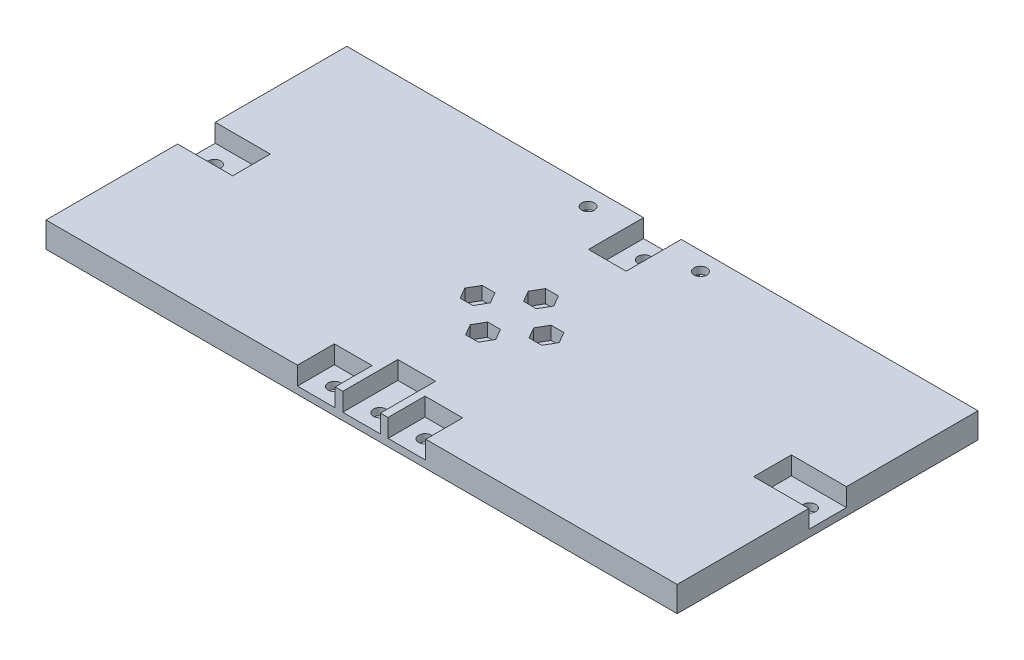
SolidWorks part; units mm, degrees
ref_plane "Front Plane" through (0, 0, 0) normal (0, 0, 1) x (1, 0, 0)
ref_plane "Top Plane" through (0, 0, 0) normal (0, 1, 0) x (1, 0, 0)
ref_plane "Right Plane" through (0, 0, 0) normal (1, 0, 0) x (0, 0, -1)
sketch "Sketch1" plane through (0, 0, 0) normal (0, 1, 0) x (1, 0, 0)
  line L1 (0, 0) -> (174.17, 0)
  line L2 (0, 0) -> (0, 83)
  line L3 (0, 83) -> (174.17, 83)
  line L4 (174.17, 0) -> (174.17, 83)
  dimension "D1" = 174.17
  dimension "D2" = 83
extrude "Boss-Extrude1" add sketch "Sketch1" along normal blind 7
sketch "Sketch2" plane through (0, 7, 0) normal (0, 1, 0) x (1, 0, 0)
  line L0 (0, 83) -> (174.17, 0) construction
  line L1 (77.585, 41.5) -> (96.585, 41.5) construction
  line L2 (87.085, 49.5) -> (87.085, 33.5) construction
  circle A0 centre (87.085, 49.5) radius 1.75
  circle A1 centre (77.585, 41.5) radius 1.75
  circle A2 centre (96.585, 41.5) radius 1.75
  circle A3 centre (87.085, 33.5) radius 1.75
  point P8 (87.085, 41.5)
  point P9 (87.085, 41.5)
  point P10 (87.085, 41.5)
  dimension "D3" = 3.5
  dimension "D1" = 19
  dimension "D2" = 16
extrude "Cut-Extrude1" cut sketch "Sketch2" against normal through all
sketch "Sketch3" plane through (0, 7, 0) normal (0, 1, 0) x (1, 0, 0)
  line L0 (0, 83) -> (174.17, 0) construction
  line L1 (5, 41.5) -> (169.17, 41.5) construction
  line L2 (87.085, 78) -> (87.085, 5) construction
  circle A0 centre (87.085, 78) radius 1.75
  circle A1 centre (5, 41.5) radius 1.75
  circle A2 centre (87.085, 5) radius 1.75
  circle A3 centre (169.17, 41.5) radius 1.75
  point P8 (87.085, 41.5)
  point P9 (87.085, 41.5)
  point P11 (87.085, 41.5)
  dimension "D3" = 3.5
  dimension "D1" = 164.17
  dimension "D2" = 73
extrude "Cut-Extrude2" cut sketch "Sketch3" against normal through all
sketch "Sketch4" plane through (0, 7, 0) normal (0, 1, 0) x (1, 0, 0)
  line L0 (0, 83) -> (0, 0) construction
  line L1 (0, 46.5) -> (15, 46.5) construction
  line L2 (0, 46.5) -> (0, 36.5) construction
  line L3 (0, 36.5) -> (15, 36.5) construction
  line L4 (15, 46.5) -> (15, 36.5) construction
  line L5 (0, 0) -> (174.17, 0) construction
  line L6 (82.085, 0) -> (92.085, 0) construction
  line L7 (82.085, 0) -> (82.085, 15) construction
  line L8 (82.085, 15) -> (92.085, 15) construction
  line L9 (92.085, 0) -> (92.085, 15) construction
  line L10 (174.17, 83) -> (0, 83) construction
  line L11 (92.085, 83) -> (82.085, 83) construction
  line L12 (92.085, 83) -> (92.085, 68) construction
  line L13 (92.085, 68) -> (82.085, 68) construction
  line L14 (82.085, 83) -> (82.085, 68) construction
  line L15 (174.17, 0) -> (174.17, 83) construction
  line L16 (174.17, 36.5) -> (159.17, 36.5) construction
  line L17 (174.17, 36.5) -> (174.17, 46.5) construction
  line L18 (174.17, 46.5) -> (159.17, 46.5) construction
  line L19 (159.17, 36.5) -> (159.17, 46.5) construction
  line L20 (0, 41.5) -> (174.17, 41.5) construction
  line L21 (87.085, 83) -> (87.085, 0) construction
  line L22 (-0.2, 46.7) -> (15.2, 46.7)
  line L23 (15.2, 46.7) -> (15.2, 36.3)
  line L24 (-0.2, 36.3) -> (15.2, 36.3)
  line L25 (-0.2, 46.7) -> (-0.2, 36.3)
  line L26 (81.885, 15.2) -> (92.285, 15.2)
  line L27 (92.285, -0.2) -> (92.285, 15.2)
  line L28 (81.885, -0.2) -> (92.285, -0.2)
  line L29 (81.885, -0.2) -> (81.885, 15.2)
  line L30 (81.885, 83.2) -> (81.885, 67.8)
  line L31 (92.285, 67.8) -> (81.885, 67.8)
  line L32 (92.285, 83.2) -> (92.285, 67.8)
  line L33 (92.285, 83.2) -> (81.885, 83.2)
  line L34 (174.37, 46.7) -> (158.97, 46.7)
  line L35 (158.97, 36.3) -> (158.97, 46.7)
  line L36 (174.37, 36.3) -> (158.97, 36.3)
  line L37 (174.37, 36.3) -> (174.37, 46.7)
  point P26 (87.085, 0)
  point P27 (0, 41.5)
  point P28 (87.085, 83)
  point P29 (174.17, 41.5)
  dimension "D1" = 15
  dimension "D2" = 10
  dimension "D3" = 0.2
extrude "Cut-Extrude3" cut sketch "Sketch4" against normal blind 5
sketch "Sketch5" plane through (0, 7, 0) normal (0, 1, 0) x (1, 0, 0)
  line L0 (0, 0) -> (81.885, 0) construction
  line L6 (79.585, 10) -> (79.585, 0) construction
  line L7 (79.585, 0) -> (69.585, 0) construction
  line L9 (79.585, 10) -> (69.585, 10) construction
  line L10 (69.585, 0) -> (69.585, 10) construction
  line L11 (94.585, 0) -> (104.585, 0) construction
  line L13 (94.585, 10) -> (104.585, 10) construction
  line L14 (104.585, 0) -> (104.585, 10) construction
  line L16 (92.285, 0) -> (174.17, 0) construction
  line L17 (94.585, 10) -> (94.585, 0) construction
  line L18 (79.585, 0) -> (94.585, 0) construction
  line L22 (87.085, 83) -> (87.085, 0) construction
  line L23 (92.285, 83) -> (81.885, 83) construction
  line L24 (79.785, 10.2) -> (69.385, 10.2)
  line L25 (69.385, -0.2) -> (69.385, 10.2)
  line L26 (79.785, -0.2) -> (69.385, -0.2)
  line L27 (79.785, 10.2) -> (79.785, -0.2)
  line L28 (94.385, 10.2) -> (104.785, 10.2)
  line L29 (104.785, -0.2) -> (104.785, 10.2)
  line L30 (94.385, -0.2) -> (104.785, -0.2)
  line L31 (94.385, 10.2) -> (94.385, -0.2)
  point P2 (87.085, 0)
  dimension "D1" = 15
  dimension "D2" = 0.2
  dimension "D3" = 10
  dimension "D4" = 10
  dimension "D5" = 10
  dimension "D6" = 10
extrude "Cut-Extrude4" cut sketch "Sketch5" against normal blind 5
sketch "Sketch6" plane through (0, 2, 0) normal (0, 1, 0) x (1, 0, 0)
  line L0 (74.585, 0) -> (74.585, 5) construction
  line L1 (79.785, 0) -> (69.385, 0) construction
  line L2 (99.585, 0) -> (99.585, 5) construction
  line L3 (94.385, 0) -> (104.785, 0) construction
  circle A0 centre (74.585, 5) radius 1.75
  circle A1 centre (99.585, 5) radius 1.75
  dimension "D3" = 3.5
  dimension "D4" = 3.5
  dimension "D1" = 5
  dimension "D2" = 5
extrude "Cut-Extrude5" cut sketch "Sketch6" against normal through all
sketch "Sketch7" plane through (0, 7, 0) normal (0, 1, 0) x (1, 0, 0)
  line L0 (75.8241, 44.55) -> (79.3459, 44.55)
  line L1 (79.3459, 44.55) -> (81.1068, 41.5)
  line L2 (81.1068, 41.5) -> (79.3459, 38.45)
  line L3 (79.3459, 38.45) -> (75.8241, 38.45)
  line L4 (75.8241, 38.45) -> (74.0632, 41.5)
  line L5 (74.0632, 41.5) -> (75.8241, 44.55)
  line L6 (87.085, 33.5) -> (87.085, 49.5) construction
  line L7 (85.3241, 52.55) -> (88.8459, 52.55)
  line L8 (88.8459, 52.55) -> (90.6068, 49.5)
  line L9 (90.6068, 49.5) -> (88.8459, 46.45)
  line L10 (88.8459, 46.45) -> (85.3241, 46.45)
  line L11 (85.3241, 46.45) -> (83.5632, 49.5)
  line L12 (83.5632, 49.5) -> (85.3241, 52.55)
  line L13 (77.585, 41.5) -> (96.585, 41.5) construction
  line L14 (100.1068, 41.5) -> (98.3459, 44.55)
  line L15 (98.3459, 38.45) -> (100.1068, 41.5)
  line L16 (94.8241, 38.45) -> (98.3459, 38.45)
  line L17 (93.0632, 41.5) -> (94.8241, 38.45)
  line L18 (94.8241, 44.55) -> (93.0632, 41.5)
  line L19 (98.3459, 44.55) -> (94.8241, 44.55)
  line L20 (83.5632, 33.5) -> (85.3241, 30.45)
  line L21 (85.3241, 36.55) -> (83.5632, 33.5)
  line L22 (88.8459, 36.55) -> (85.3241, 36.55)
  line L23 (90.6068, 33.5) -> (88.8459, 36.55)
  line L24 (88.8459, 30.45) -> (90.6068, 33.5)
  line L25 (85.3241, 30.45) -> (88.8459, 30.45)
  circle A1 centre (77.585, 41.5) radius 3.5218 construction
  circle A2 centre (87.085, 49.5) radius 3.5218 construction
  circle A3 centre (96.585, 41.5) radius 3.5218 construction
  circle A4 centre (87.085, 33.5) radius 3.5218 construction
  point P11 (77.585, 38.45)
  point P24 (87.085, 46.45)
  dimension "D1" = 120
  dimension "D2" = 6.1
  dimension "D3" = 120
  dimension "D4" = 6.1
extrude "Cut-Extrude6" cut sketch "Sketch7" against normal blind 3.64
sketch "Sketch9" plane through (0, 0, 0) normal (0, -1, 0) x (1, 0, 0)
  line L0 (174.17, -83) -> (0, -83) construction
  line L1 (66.585, -83) -> (76.585, -83) construction
  line L2 (66.585, -83) -> (66.585, -73) construction
  line L3 (66.585, -73) -> (76.585, -73) construction
  line L4 (76.585, -83) -> (76.585, -73) construction
  line L5 (66.585, -73) -> (76.585, -83) construction
  line L6 (97.585, -83) -> (107.585, -83) construction
  line L7 (97.585, -83) -> (97.585, -73) construction
  line L8 (97.585, -73) -> (107.585, -73) construction
  line L9 (107.585, -83) -> (107.585, -73) construction
  line L10 (97.585, -73) -> (107.585, -83) construction
  line L11 (66.385, -72.8) -> (76.785, -72.8)
  line L12 (76.785, -83.2) -> (76.785, -72.8)
  line L13 (66.385, -83.2) -> (76.785, -83.2)
  line L14 (66.385, -83.2) -> (66.385, -72.8)
  line L15 (97.385, -72.8) -> (107.785, -72.8)
  line L16 (107.785, -83.2) -> (107.785, -72.8)
  line L17 (97.385, -83.2) -> (107.785, -83.2)
  line L18 (97.385, -83.2) -> (97.385, -72.8)
  line L19 (87.085, -83) -> (87.085, 0) construction
  line L20 (0, 0) -> (174.17, 0) construction
  line L21 (102.585, -78) -> (71.585, -78) construction
  point P10 (71.585, -78)
  point P11 (102.585, -78)
  point P12 (87.085, -78)
  dimension "D1" = 10
  dimension "D2" = 10
  dimension "D3" = 31
  dimension "D5" = 0.2
extrude "Cut-Extrude7" cut sketch "Sketch9" against normal blind 5
sketch "Sketch10" plane through (0, 5, 0) normal (0, -1, 0) x (1, 0, 0)
  line L0 (66.585, -73) -> (76.585, -83) construction
  line L1 (97.585, -73) -> (107.585, -83) construction
  circle A0 centre (71.585, -78) radius 1.75
  circle A1 centre (102.585, -78) radius 1.75
  dimension "D1" = 3.5
extrude "Cut-Extrude8" cut sketch "Sketch10" against normal through all
